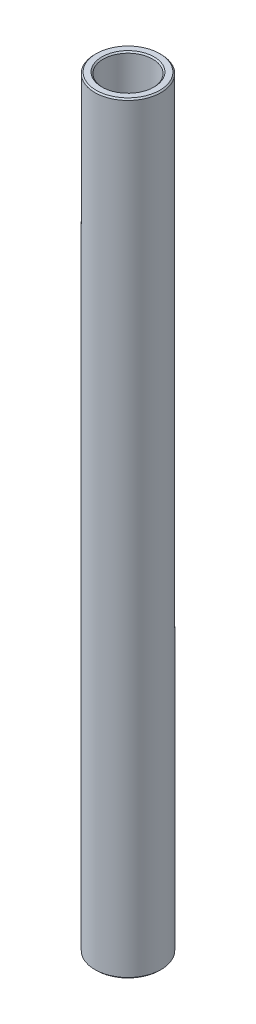
SolidWorks part; units mm, degrees
ref_plane "Front Plane" through (0, 0, 0) normal (0, 0, 1) x (1, 0, 0)
ref_plane "Top Plane" through (0, 0, 0) normal (0, 1, 0) x (1, 0, 0)
ref_plane "Right Plane" through (0, 0, 0) normal (1, 0, 0) x (0, 0, -1)
sketch "Sketch1" plane through (0, 0, 0) normal (0, 0, 1) x (1, 0, 0)
  line L0 (0, 11.6086) -> (0, -11.6086) construction
  line L1 (4.7625, 73.1171) -> (6.35, 73.1171)
  line L2 (6.35, 73.1171) -> (6.35, -73.1171)
  line L3 (6.35, -73.1171) -> (4.7625, -73.1171)
  line L4 (4.7625, -73.1171) -> (4.7625, 73.1171)
  line L5 (4.7625, 0) -> (0, 0) construction
  dimension "D1" = 9.525
  dimension "D2" = 12.7
  dimension "D3" = 146.2342
revolve "Revolve1" add sketch "Sketch1" angle 360 about L0
chamfer "Chamfer1" distance 0.254 angle 45 4 edges at (-4.7625, -73.1171, 0) (-6.35, -73.1171, 0) (-6.35, 73.1171, 0) (-4.7625, 73.1171, 0)
